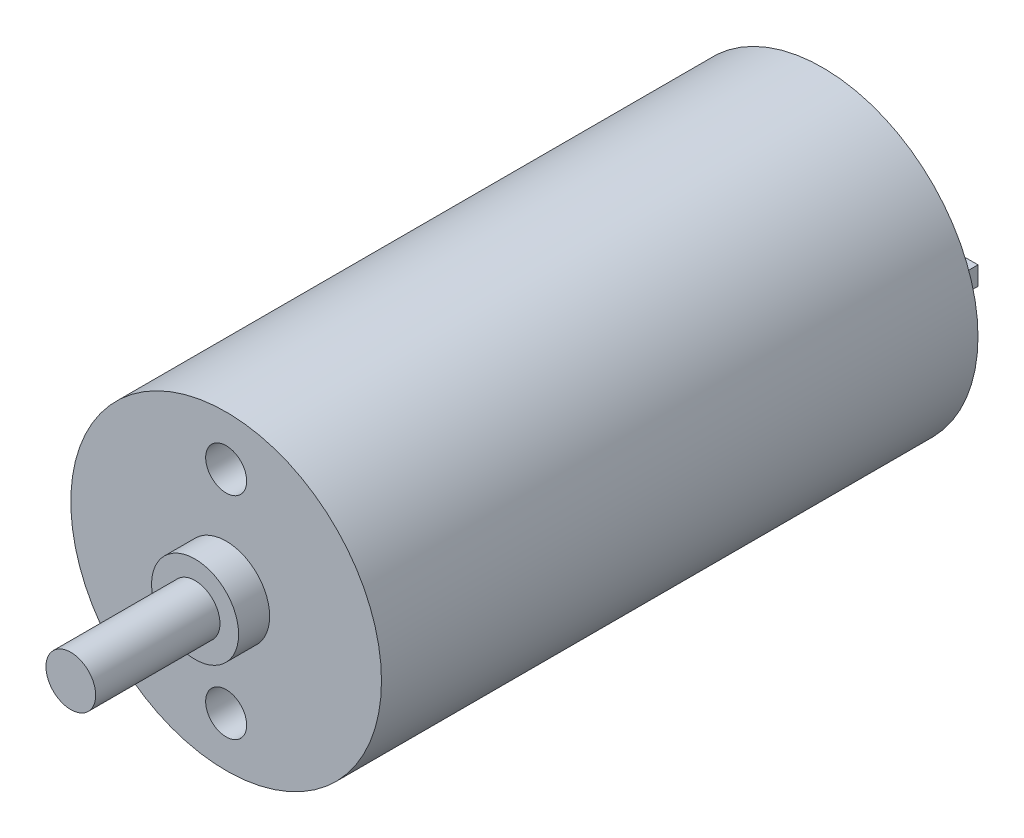
SolidWorks part; units mm, degrees
ref_plane "Přední rovina" through (0, 0, 0) normal (0, 0, 1) x (1, 0, 0)
ref_plane "Horní rovina" through (0, 0, 0) normal (0, 1, 0) x (1, 0, 0)
ref_plane "Pravá rovina" through (0, 0, 0) normal (1, 0, 0) x (0, 0, -1)
sketch "Skica1" plane through (0, 0, 0) normal (0, 0, 1) x (1, 0, 0)
  circle A0 centre (0, 0) radius 12.5
  dimension "D1" = 25
extrude "Přidat vysunutím1" add sketch "Skica1" along normal blind 48
sketch "Skica2" plane through (0, 0, 48) normal (0, 0, 1) x (1, 0, 0)
  circle A0 centre (0, 0) radius 3.5
  dimension "D1" = 7
extrude "Přidat vysunutím2" add sketch "Skica2" along normal blind 2.5
sketch "Skica3" plane through (0, 0, 50.5) normal (0, 0, 1) x (1, 0, 0)
  circle A0 centre (0, 0) radius 2
  dimension "D1" = 4
extrude "Přidat vysunutím3" add sketch "Skica3" along normal blind 10
sketch "Skica4" plane through (0, 0, 0) normal (0, 0, -1) x (-1, 0, 0)
  line L1 (-8.5, 1) -> (-4.5, 1)
  line L2 (-8.5, 1) -> (-8.5, -0.5)
  line L3 (-8.5, -0.5) -> (-4.5, -0.5)
  line L4 (-4.5, 1) -> (-4.5, -0.5)
  line L5 (4.5, 1) -> (8.5, 1)
  line L6 (4.5, 1) -> (4.5, -0.5)
  line L7 (4.5, -0.5) -> (8.5, -0.5)
  line L8 (8.5, 1) -> (8.5, -0.5)
  dimension "D1" = 4
  dimension "D2" = 4
  dimension "D3" = 1.5
  dimension "D4" = 1.5
  dimension "D5" = 4.5
  dimension "D6" = 4.5
  dimension "D7" = 0.5
  dimension "D8" = 0.5
extrude "Přidat vysunutím4" add sketch "Skica4" along normal blind 4
sketch "Skica5" plane through (0, 0, 48) normal (0, 0, 1) x (1, 0, 0)
  circle A0 centre (0, 8.5) radius 1.65
  circle A1 centre (0, -8.5) radius 1.65
  dimension "D3" = 3.3
  dimension "D4" = 3.3
  dimension "D1" = 8.5
  dimension "D2" = 8.5
extrude "Odebrat vysunutím1" cut sketch "Skica5" against normal blind 4
